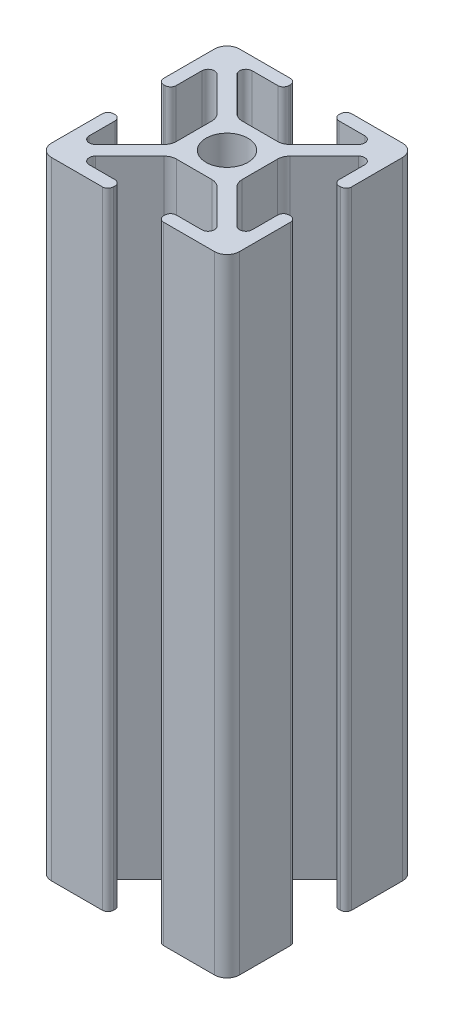
SolidWorks part; units mm, degrees
material "Aleación 1060"
ref_plane "Front Plane" through (0, 0, 0) normal (0, 0, 1) x (1, 0, 0)
ref_plane "Top Plane" through (0, 0, 0) normal (0, 1, 0) x (1, 0, 0)
ref_plane "Right Plane" through (0, 0, 0) normal (1, 0, 0) x (0, 0, -1)
sketch "Sketch1" plane through (0, 0, 0) normal (0, 1, 0) x (1, 0, 0)
  line L10 (14.1, -4) -> (13.9, -4)
  line L11 (11.2929, -9.6929) -> (5.8358, -4.2358)
  line L12 (5.25, -2.8216) -> (5.25, 2.8216)
  line L13 (5.8358, 4.2358) -> (11.2929, 9.6929)
  line L14 (9.6929, 11.2929) -> (4.2358, 5.8358)
  line L15 (2.8216, 5.25) -> (-2.8216, 5.25)
  line L16 (-4.2358, 5.8358) -> (-9.6929, 11.2929)
  line L17 (-11.2929, 9.6929) -> (-5.8358, 4.2358)
  line L18 (-5.25, 2.8216) -> (-5.25, -2.8216)
  line L19 (-5.8358, -4.2358) -> (-11.2929, -9.6929)
  line L20 (-9.6929, -11.2929) -> (-4.2358, -5.8358)
  line L21 (-2.8216, -5.25) -> (2.8216, -5.25)
  line L22 (4.2358, -5.8358) -> (9.6929, -11.2929)
  line L23 (8.9858, -13) -> (4.9, -13)
  line L24 (4, -13.9) -> (4, -14.1)
  line L25 (15, -4.9) -> (15, -13)
  line L26 (4.9, -15) -> (13, -15)
  line L27 (13, -8.9858) -> (13, -4.9)
  line L28 (14.1, 4) -> (13.9, 4)
  line L29 (8.9858, 13) -> (4.9, 13)
  line L30 (4, 13.9) -> (4, 14.1)
  line L31 (4.9, 15) -> (13, 15)
  line L32 (15, 4.9) -> (15, 13)
  line L33 (13, 8.9858) -> (13, 4.9)
  line L34 (-14.1, -4) -> (-13.9, -4)
  line L35 (-8.9858, -13) -> (-4.9, -13)
  line L36 (-4, -13.9) -> (-4, -14.1)
  line L37 (-4.9, -15) -> (-13, -15)
  line L38 (-15, -4.9) -> (-15, -13)
  line L39 (-13, -8.9858) -> (-13, -4.9)
  line L40 (-14.1, 4) -> (-13.9, 4)
  line L41 (-8.9858, 13) -> (-4.9, 13)
  line L42 (-4, 13.9) -> (-4, 14.1)
  line L43 (-4.9, 15) -> (-13, 15)
  line L44 (-15, 4.9) -> (-15, 13)
  line L45 (-13, 8.9858) -> (-13, 4.9)
  circle A17 centre (0, 0) radius 3.35
  arc A18 (11.2929, -9.6929) -> (13, -8.9858) centre (12, -8.9858) ccw
  arc A19 (5.25, -2.8216) -> (5.8358, -4.2358) centre (7.25, -2.8216) ccw
  arc A20 (5.8358, 4.2358) -> (5.25, 2.8216) centre (7.25, 2.8216) ccw
  arc A21 (13, 8.9858) -> (11.2929, 9.6929) centre (12, 8.9858) ccw
  arc A22 (9.6929, 11.2929) -> (8.9858, 13) centre (8.9858, 12) ccw
  arc A23 (2.8216, 5.25) -> (4.2358, 5.8358) centre (2.8216, 7.25) ccw
  arc A24 (-4.2358, 5.8358) -> (-2.8216, 5.25) centre (-2.8216, 7.25) ccw
  arc A25 (-8.9858, 13) -> (-9.6929, 11.2929) centre (-8.9858, 12) ccw
  arc A26 (-11.2929, 9.6929) -> (-13, 8.9858) centre (-12, 8.9858) ccw
  arc A27 (-5.25, 2.8216) -> (-5.8358, 4.2358) centre (-7.25, 2.8216) ccw
  arc A28 (-5.8358, -4.2358) -> (-5.25, -2.8216) centre (-7.25, -2.8216) ccw
  arc A29 (-13, -8.9858) -> (-11.2929, -9.6929) centre (-12, -8.9858) ccw
  arc A30 (-9.6929, -11.2929) -> (-8.9858, -13) centre (-8.9858, -12) ccw
  arc A31 (-2.8216, -5.25) -> (-4.2358, -5.8358) centre (-2.8216, -7.25) ccw
  arc A32 (4.2358, -5.8358) -> (2.8216, -5.25) centre (2.8216, -7.25) ccw
  arc A33 (8.9858, -13) -> (9.6929, -11.2929) centre (8.9858, -12) ccw
  arc A34 (13.9, -4) -> (13, -4.9) centre (13.9, -4.9) ccw
  arc A35 (15, -4.9) -> (14.1, -4) centre (14.1, -4.9) ccw
  arc A36 (4.9, -13) -> (4, -13.9) centre (4.9, -13.9) ccw
  arc A37 (4, -14.1) -> (4.9, -15) centre (4.9, -14.1) ccw
  arc A38 (13, -15) -> (15, -13) centre (13, -13) ccw
  arc A39 (13, 4.9) -> (13.9, 4) centre (13.9, 4.9) ccw
  arc A40 (4, 13.9) -> (4.9, 13) centre (4.9, 13.9) ccw
  arc A41 (4.9, 15) -> (4, 14.1) centre (4.9, 14.1) ccw
  arc A42 (15, 13) -> (13, 15) centre (13, 13) ccw
  arc A43 (14.1, 4) -> (15, 4.9) centre (14.1, 4.9) ccw
  arc A44 (-13, -4.9) -> (-13.9, -4) centre (-13.9, -4.9) ccw
  arc A45 (-4, -13.9) -> (-4.9, -13) centre (-4.9, -13.9) ccw
  arc A46 (-4.9, -15) -> (-4, -14.1) centre (-4.9, -14.1) ccw
  arc A47 (-15, -13) -> (-13, -15) centre (-13, -13) ccw
  arc A48 (-14.1, -4) -> (-15, -4.9) centre (-14.1, -4.9) ccw
  arc A49 (-13.9, 4) -> (-13, 4.9) centre (-13.9, 4.9) ccw
  arc A50 (-4.9, 13) -> (-4, 13.9) centre (-4.9, 13.9) ccw
  arc A51 (-4, 14.1) -> (-4.9, 15) centre (-4.9, 14.1) ccw
  arc A52 (-13, 15) -> (-15, 13) centre (-13, 13) ccw
  arc A53 (-15, 4.9) -> (-14.1, 4) centre (-14.1, 4.9) ccw
  point P48 (0, 0.001)
  point P49 (0.001, 0.001)
  point P50 (0.001, 0)
extrude "Extrusion" add sketch "Sketch1" against normal blind 100
other "PropertyManager"
